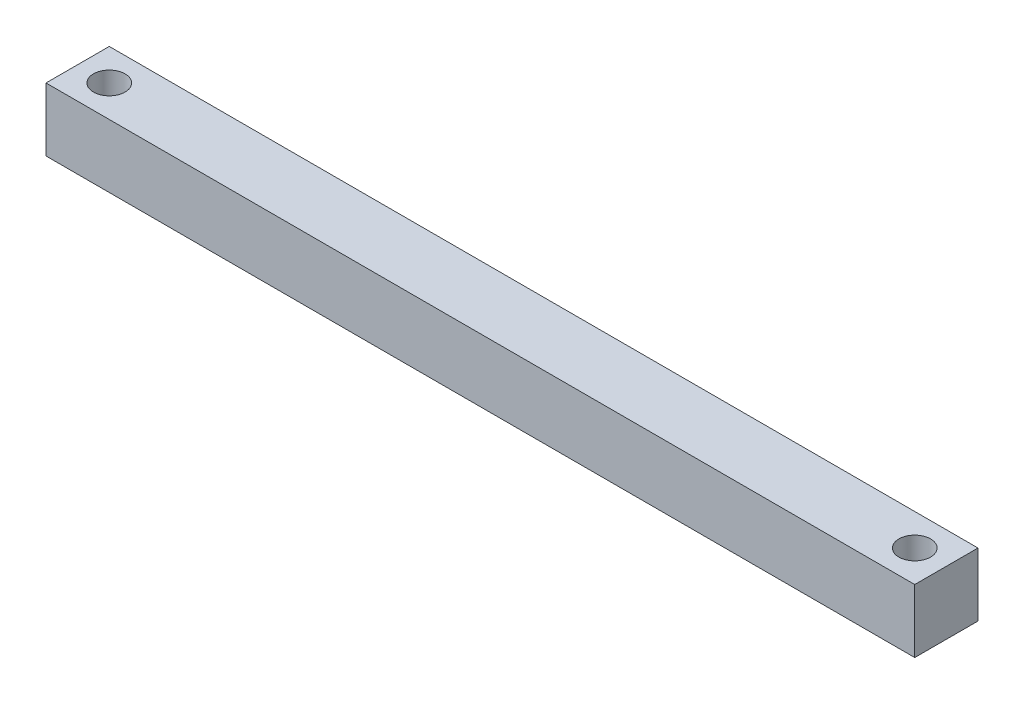
SolidWorks part; units mm, degrees
ref_plane "Front Plane" through (0, 0, 0) normal (0, 0, 1) x (1, 0, 0)
ref_plane "Top Plane" through (0, 0, 0) normal (0, 1, 0) x (1, 0, 0)
ref_plane "Right Plane" through (0, 0, 0) normal (1, 0, 0) x (0, 0, -1)
sketch "Sketch1" plane through (0, 0, 0) normal (1, 0, 0) x (0, 0, -1)
  line L1 (-12.7, -12.7) -> (12.7, -12.7)
  line L2 (-12.7, -12.7) -> (-12.7, 12.7)
  line L3 (-12.7, 12.7) -> (12.7, 12.7)
  line L4 (12.7, -12.7) -> (12.7, 12.7)
  line L5 (-12.7, -12.7) -> (12.7, 12.7) construction
  line L6 (-12.7, 12.7) -> (12.7, -12.7) construction
  point P0 (0, 0)
  dimension "D1" = 25.4
  dimension "D2" = 25.4
extrude "Boss-Extrude1" add sketch "Sketch1" against normal blind 348.8291
sketch "Sketch2" plane through (0, 12.7, 0) normal (0, 1, 0) x (1, 0, 0)
  line L0 (-348.8291, 12.7) -> (-348.8291, -12.7) construction
  line L1 (-174.4145, 12.7) -> (-174.4145, -12.7) construction
  line L2 (-348.8291, 12.7) -> (0, 12.7) construction
  line L3 (-348.8291, -12.7) -> (0, -12.7) construction
  circle A0 centre (-336.1291, 0) radius 6.35
  circle A1 centre (-12.7, 0) radius 6.35
  dimension "D1" = 12.7
  dimension "D2" = 12.7
extrude "Cut-Extrude1" cut sketch "Sketch2" against normal through all
equation "\"D1@Boss-Extrude1\"=13.55+(2*(1.75*(cotan( 87))))"
